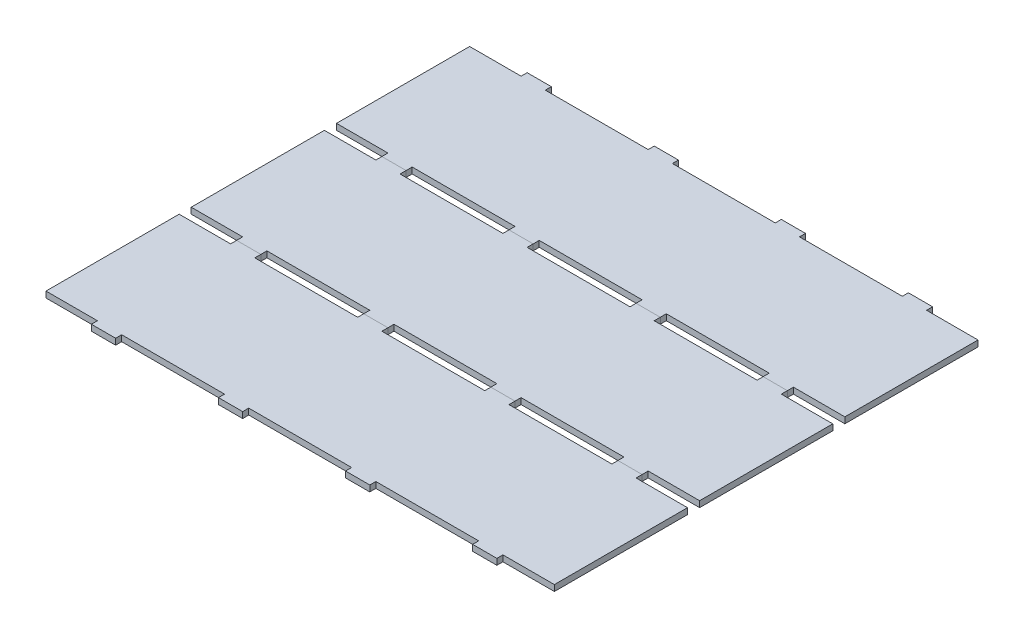
SolidWorks part; units mm, degrees
material "Cedar"
ref_plane "Front Plane" through (0, 0, 0) normal (0, 0, 1) x (1, 0, 0)
ref_plane "Top Plane" through (0, 0, 0) normal (0, 1, 0) x (1, 0, 0)
ref_plane "Right Plane" through (0, 0, 0) normal (1, 0, 0) x (0, 0, -1)
sketch "Sketch1" plane through (0, 0, 0) normal (0, 1, 0) x (1, 0, 0)
  line L1 (-266.7, 76.2) -> (266.7, 76.2)
  line L2 (-266.7, 76.2) -> (-266.7, -76.2)
  line L3 (-266.7, -76.2) -> (266.7, -76.2)
  line L4 (266.7, 76.2) -> (266.7, -76.2)
  line L5 (-266.7, 76.2) -> (266.7, -76.2) construction
  line L6 (-266.7, -76.2) -> (266.7, 76.2) construction
  point P0 (0, 0)
  dimension "D1" = 152.4
  dimension "D2" = 533.4
extrude "Boss-Extrude1" add sketch "Sketch1" along normal blind 6.35
sketch "Sketch2" plane through (0, 6.35, 0) normal (0, 1, 0) x (1, 0, 0)
  line L0 (-266.7, -69.85) -> (266.7, -69.85) construction
  line L1 (-266.7, 76.2) -> (-266.7, -76.2) construction
  line L2 (266.7, -76.2) -> (266.7, 76.2) construction
  line L3 (-266.7, -76.2) -> (266.7, -76.2) construction
  line L5 (-53.975, -69.85) -> (53.975, -69.85)
  line L6 (-53.975, -69.85) -> (-53.975, -76.2)
  line L7 (-53.975, -76.2) -> (53.975, -76.2)
  line L8 (53.975, -69.85) -> (53.975, -76.2)
  line L9 (-53.975, -69.85) -> (53.975, -76.2) construction
  line L10 (-53.975, -76.2) -> (53.975, -69.85) construction
  point P8 (0, -73.025)
  point P14 (0, -69.85)
  point P18 (0, -69.85)
  dimension "D1" = 6.35
  dimension "D2" = 107.95
extrude "Cut-Extrude2" cut sketch "Sketch2" against normal through all
pattern_linear "LPattern1" count 3 spacing 133.35 along (-1, 0, 0) count 3 spacing 133.35 along (1, 0, 0) of "Cut-Extrude2"
mirror "Mirror2" about plane through (0, 0, 0) normal (0, 0, 1) of "LPattern1", "Cut-Extrude2"
pattern_linear "LPattern2" count 3 spacing 152.4 along (0, 0, 1) of bodies 106
